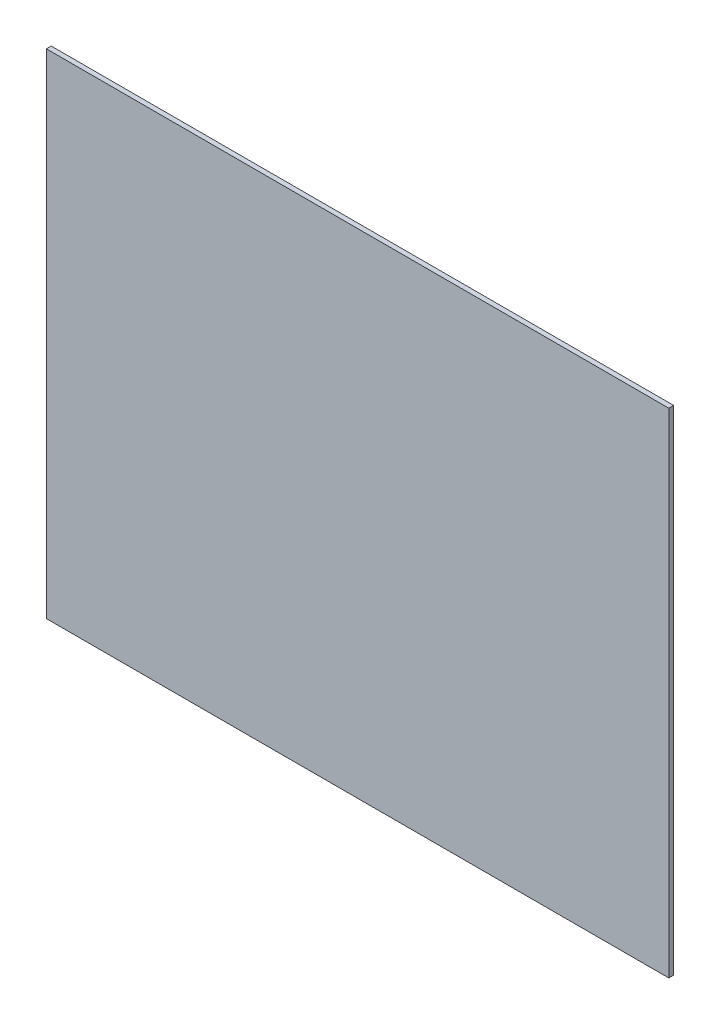
SolidWorks part; units mm, degrees
material "Acrylic (Medium-high impact)"
ref_plane "Front Plane" through (0, 0, 0) normal (0, 0, 1) x (1, 0, 0)
ref_plane "Top Plane" through (0, 0, 0) normal (0, 1, 0) x (1, 0, 0)
ref_plane "Right Plane" through (0, 0, 0) normal (1, 0, 0) x (0, 0, -1)
sketch "Sketch1" plane through (0, 0, 0) normal (0, 0, 1) x (1, 0, 0)
  line L1 (-289.5, -229.5) -> (289.5, -229.5)
  line L2 (-289.5, -229.5) -> (-289.5, 229.5)
  line L3 (-289.5, 229.5) -> (289.5, 229.5)
  line L4 (289.5, -229.5) -> (289.5, 229.5)
  line L5 (-289.5, -229.5) -> (289.5, 229.5) construction
  line L6 (-289.5, 229.5) -> (289.5, -229.5) construction
  point P0 (0, 0)
  dimension "D1" = 579
  dimension "D2" = 459
extrude "Boss-Extrude1" add sketch "Sketch1" along normal mid plane 4.4958
